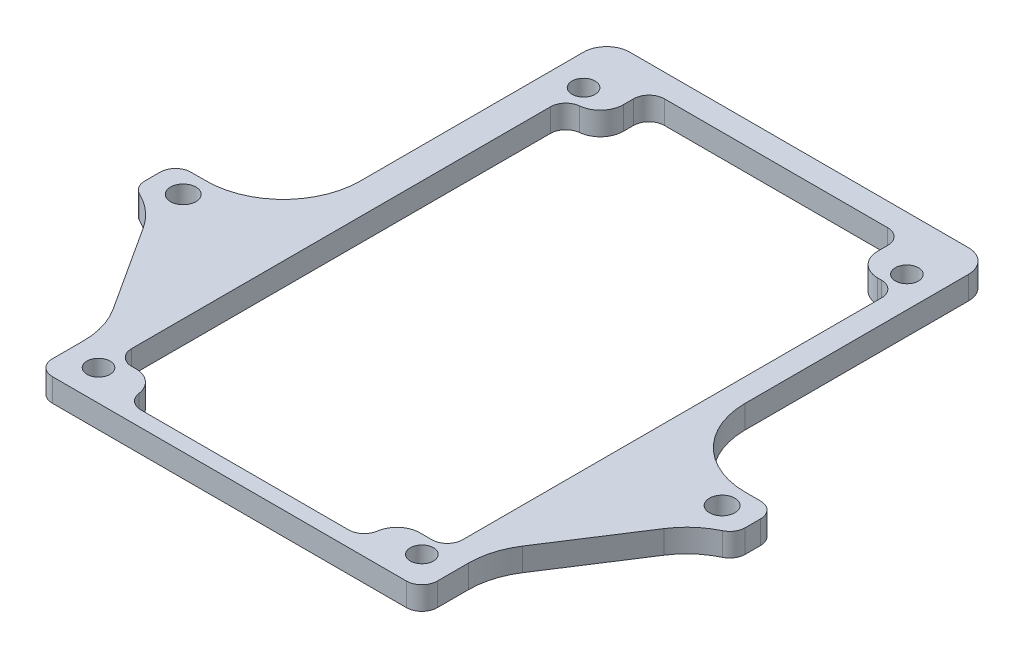
SolidWorks part; units mm, degrees
material "A-玻璃纤维"
ref_plane "前视基准面" through (0, 0, 0) normal (0, 0, 1) x (1, 0, 0)
ref_plane "上视基准面" through (0, 0, 0) normal (0, 1, 0) x (1, 0, 0)
ref_plane "右视基准面" through (0, 0, 0) normal (1, 0, 0) x (0, 0, -1)
sketch "草图1" plane through (0, 0, 0) normal (0, 1, 0) x (1, 0, 0)
  line L0 (0, 0) -> (0, 76.0272) construction
  line L1 (0, 0) -> (35, 0) construction
  line L2 (21, -25) -> (21, 38) construction
  line L3 (-37, 3) -> (-35, 3)
  line L8 (-16.5, 42) -> (16.5, 42)
  line L9 (16.5, 42) -> (16.5, 35.7)
  line L10 (-25, 13) -> (-25, 42)
  line L11 (-23, 42) -> (23, 42) construction
  line L12 (-39, 1) -> (-39, -1)
  line L13 (-37, -3) -> (-35, -3)
  line L14 (-25, -13) -> (-25, -27)
  line L15 (-23, -29) -> (-0.3296, -29)
  line L16 (23, -29) -> (-0.3296, -29)
  line L17 (25, -13) -> (25, -27)
  line L18 (25, 13) -> (25, 42)
  line L19 (39, 1) -> (39, -1)
  line L20 (37, -3) -> (35, -3)
  line L21 (37, 3) -> (35, 3)
  line L35 (16.5, 35.7) -> (22, 35.7)
  line L36 (22, 35.7) -> (22, -22.7)
  line L37 (22, -22.7) -> (15.5, -22.7)
  line L38 (15.5, -22.7) -> (15.5, -27)
  line L39 (15.5, -27) -> (-15.5, -27)
  line L40 (-15.5, -27) -> (-15.5, -22.7)
  line L41 (-15.5, -22.7) -> (-21, -22.7)
  line L42 (-21, -22.7) -> (-21, 35.7)
  line L43 (-21, 35.7) -> (-16.5, 35.7)
  line L44 (-16.5, 35.7) -> (-16.5, 42)
  line L45 (0, -27) -> (0, 0) construction
  line L46 (-22, 45) -> (22, 45)
  circle A0 centre (35, 0) radius 1.65
  circle A1 centre (-35, 0) radius 1.65
  circle A2 centre (21, 38) radius 1.5
  circle A3 centre (21, -25) radius 1.5
  circle A4 centre (-21, 38) radius 1.5
  circle A5 centre (-21, -25) radius 1.5
  arc A10 (-35, -3) -> (-25, -13) centre (-35, -13) cw
  arc A11 (-35, 3) -> (-25, 13) centre (-35, 13) ccw
  arc A12 (35, 3) -> (25, 13) centre (35, 13) cw
  arc A13 (35, -3) -> (25, -13) centre (35, -13) ccw
  arc A16 (-25, -27) -> (-23, -29) centre (-23, -27) ccw
  arc A17 (23, -29) -> (25, -27) centre (23, -27) ccw
  arc A18 (39, -1) -> (37, -3) centre (37, -1) cw
  arc A19 (39, 1) -> (37, 3) centre (37, 1) ccw
  arc A20 (-39, -1) -> (-37, -3) centre (-37, -1) ccw
  arc A21 (-37, 3) -> (-39, 1) centre (-37, 1) ccw
  arc A26 (-25, 42) -> (-22, 45) centre (-22, 42) cw
  arc A27 (25, 42) -> (22, 45) centre (22, 42) ccw
  point P11 (0, 6)
  point P49 (0, 42)
  point P58 (25, 42)
  point P61 (-25, 42)
  point P64 (-25, -29)
  point P67 (25, -29)
  point P70 (39, -3)
  point P73 (39, 3)
  point P76 (-39, -3)
  point P79 (-39, 3)
  dimension "D2" = 3.3
  dimension "D3" = 3
  dimension "D4" = 42
  dimension "D5" = 63
  dimension "D6" = 25
  dimension "D7" = 33
  dimension "D10" = 58.4
  dimension "D15" = 10
  dimension "D18" = 3
  dimension "D24" = 4
  dimension "D25" = 3
  dimension "D26" = 2
  dimension "D1" = 35
  dimension "D11" = 3
  dimension "D12" = 6
  dimension "D13" = 4
  dimension "D14" = 4
  dimension "D16" = 4
  dimension "D17" = 4
  dimension "D19" = 58.4
  dimension "D20" = 31
  dimension "D22" = 43
  dimension "D23" = 6.3
extrude "凸台-拉伸1" add sketch "草图1" along normal blind 3
fillet "圆角1" radius 2 8 edges at (-21, 1.5, 22.7) (-15.5, 1.5, 27) (15.5, 1.5, 27) (22, 1.5, 22.7) (22, 1.5, -35.7) (16.5, 1.5, -42) (-16.5, 1.5, -42) (-21, 1.5, -35.7)
sketch "草图2" plane through (0, 3, 0) normal (0, 1, 0) x (1, 0, 0)
  line L0 (36, -3) -> (25, -20)
  line L1 (35, -3) -> (37, -3) construction
  line L2 (25, -27) -> (25, -13) construction
  line L3 (35, -3) -> (36, -3)
  line L4 (25, -13) -> (25, -20)
  line L5 (0, 0) -> (0, -16.4143) construction
  line L6 (-25, -13) -> (-25, -20)
  line L7 (-35, -3) -> (-36, -3)
  line L8 (-36, -3) -> (-25, -20)
  arc A0 (35, -3) -> (25, -13) centre (35, -13) ccw construction
  arc A1 (35, -3) -> (25, -13) centre (35, -13) ccw
  arc A2 (-35, -3) -> (-25, -13) centre (-35, -13) cw
extrude "凸台-拉伸2" add sketch "草图2" against normal up to surface (3 mm away) up to face at (-21, 0, -39.5)
fillet "圆角2" radius 10 4 edges at (36, 1.5, 3) (25, 1.5, 20) (-36, 1.5, 3) (-25, 1.5, 20)
sketch "草图3" plane through (0, 3, 0) normal (0, 1, 0) x (1, 0, 0)
  line L0 (-21, 33.7) -> (-21, -20.7) construction
  line L1 (-21, 10.5) -> (-21, 6.5)
  line L2 (22, -20.7) -> (22, 33.7) construction
  line L3 (22, 6.5) -> (22, 10.5)
  line L4 (-21, 10.5) -> (22, 10.5)
  line L5 (-21, 6.5) -> (22, 6.5)
  line L6 (-23, -29) -> (23, -29) construction
  dimension "D1" = 4
  dimension "D2" = 35.5
extrude "凸台-拉伸3" add sketch "草图3" against normal up to surface (3 mm away) up to face at (0, 0, 0.0669)
fillet "圆角3" radius 5 4 edges at (-21, 1.5, -10.5) (22, 1.5, -10.5) (22, 1.5, -6.5) (-21, 1.5, -6.5)
sketch "草图4" plane through (0, 3, 0) normal (0, 1, 0) x (1, 0, 0)
  line L0 (-21, 19.8497) -> (-21, 0)
  line L1 (-21, 33.7) -> (-21, 15.5) construction
  line L2 (-21, 1.5) -> (-21, -20.7) construction
  line L3 (-21, 0) -> (22, 0)
  line L4 (22, -20.7) -> (22, 1.5) construction
  line L5 (22, 0) -> (22, 19.8497)
  line L6 (22, 15.5) -> (22, 33.7) construction
  line L7 (22, 19.8497) -> (-21, 19.8497)
extrude "切除-拉伸1" cut sketch "草图4" against normal blind 10
fillet "圆角4" radius 3 1 edges at (16.5, 1.5, -35.7)
fillet "圆角5" radius 3 1 edges at (-16.5, 1.5, -35.7)
fillet "圆角6" radius 3 1 edges at (-15.5, 1.5, 22.7)
fillet "圆角7" radius 3 1 edges at (15.5, 1.5, 22.7)
